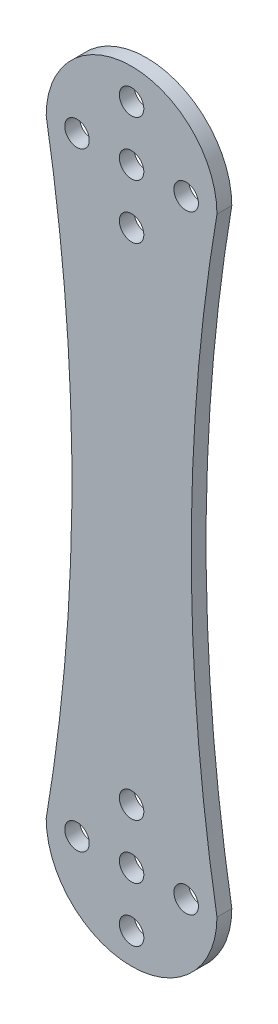
SolidWorks part; units mm, degrees
ref_plane "前视基准面" through (0, 0, 0) normal (0, 0, 1) x (1, 0, 0)
ref_plane "上视基准面" through (0, 0, 0) normal (0, 1, 0) x (1, 0, 0)
ref_plane "右视基准面" through (0, 0, 0) normal (1, 0, 0) x (0, 0, -1)
sketch "草图1" plane through (0, 0, 0) normal (0, 0, 1) x (1, 0, 0)
  line L0 (53.4306, 77.5861) -> (53.4306, -101.7916) construction
  line L1 (-16.0754, -29.3816) -> (140.1318, -29.3816) construction
  line L2 (40.2821, 11.6184) -> (68.1227, 11.6184) construction
  line L3 (40.2821, -70.3816) -> (68.1227, -70.3816) construction
  arc A0 (64.9306, 11.6184) -> (41.9306, 11.6184) centre (53.4306, 11.6184) ccw
  circle A1 centre (53.4306, 11.6184) radius 1.65
  circle A2 centre (46.0806, 11.6184) radius 1.65
  circle A3 centre (53.4306, 18.9684) radius 1.65
  circle A4 centre (60.7806, 11.6184) radius 1.65
  circle A5 centre (53.4306, 4.2684) radius 1.65
  circle A6 centre (60.7806, 11.6184) radius 1.65
  circle A7 centre (46.0806, 11.6184) radius 1.65
  circle A8 centre (53.4306, 4.2684) radius 1.65
  circle A9 centre (53.4306, 18.9684) radius 1.65
  circle A10 centre (53.4306, -70.3816) radius 1.65
  circle A11 centre (46.0806, -70.3816) radius 1.65
  circle A12 centre (53.4306, -63.0316) radius 1.65
  circle A13 centre (60.7806, -70.3816) radius 1.65
  circle A14 centre (53.4306, -77.7316) radius 1.65
  arc A15 (64.9306, -70.3816) -> (41.9306, -70.3816) centre (53.4306, -70.3816) cw
  arc A16 (41.9306, 11.6184) -> (41.9306, -70.3816) centre (-199.0083, -29.3816) cw
  arc A17 (64.9306, 11.6184) -> (64.9306, -70.3816) centre (305.8695, -29.3816) ccw
  point P31 (53.4306, 11.6184)
  dimension "D5" = 4
  dimension "D1" = 3.3
  dimension "D3" = 3.3
  dimension "D4" = 14.7
  dimension "D2" = 11.5
  dimension "D6" = 82
extrude "凸台-拉伸2" add sketch "草图1" along normal blind 2 contours A17 A0 A16 A15 A11 A5 A1 A2 A3 A4 A10 A12 A13 A14
